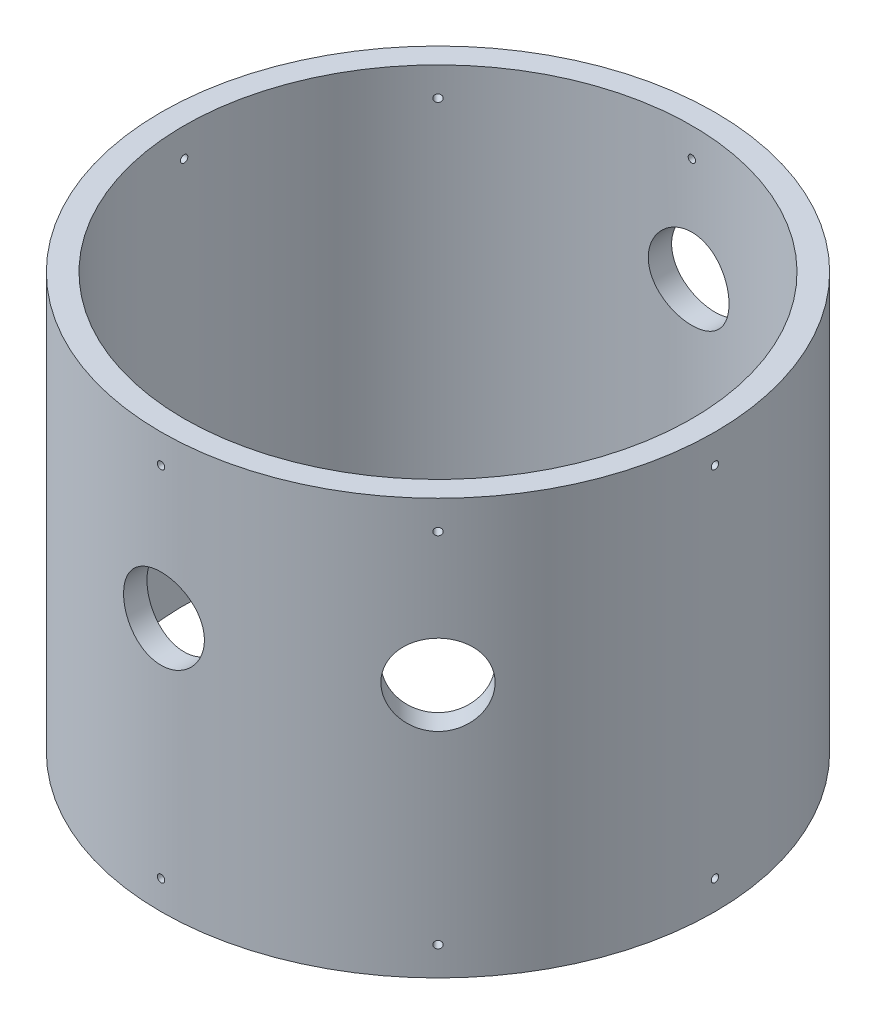
SolidWorks part; units mm, degrees
ref_plane "Front Plane" through (0, 0, 0) normal (0, 0, 1) x (1, 0, 0)
ref_plane "Top Plane" through (0, 0, 0) normal (0, 1, 0) x (1, 0, 0)
ref_plane "Right Plane" through (0, 0, 0) normal (1, 0, 0) x (0, 0, -1)
sketch "Sketch1" plane through (0, 0, 0) normal (0, 1, 0) x (1, 0, 0)
  circle A0 centre (0, 0) radius 152.4
  circle A1 centre (0, 0) radius 139.7
  dimension "D1" = 304.8
  dimension "D2" = 279.4
extrude "Boss-Extrude1" add sketch "Sketch1" along normal blind 228.6
ref_plane "Plane1" through (0, 0, 152.4) normal (0, 0, 1) x (1, 0, 0)
hole_wizard "#10-32 Tapped Hole1" positions "Sketch2" profile "Sketch3" tap size "#10-32" standard "ANSI Inch"
sketch "Sketch2" plane through (0, 0, 152.4) normal (0, 0, 1) x (1, 0, 0)
  line L0 (152.4, 228.6) -> (-152.4, 228.6) construction
  line L1 (-152.4, 0) -> (152.4, 0) construction
  line L3 (0, 212.725) -> (0, 15.875)
  line L4 (0, 15.875) -> (0, 0)
  point P0 (0, 212.725)
  point P2 (0, 15.875)
  dimension "D1" = 15.875
  dimension "D2" = 15.875
sketch "Sketch3" plane through (0, 212.725, 152.4) normal (1, 0, 0) x (0, -1, 0)
  line L0 (0, 0) -> (0, 349.967)
  line L1 (0, 349.967) -> (2.0193, 349.967)
  line L2 (2.0193, 349.967) -> (2.0193, 0)
  line L5 (2.0193, 0) -> (0, 0)
  line L11 (0, -6.35) -> (0, 107.95) construction
  dimension "Thread Major Dia." = 4.0386
  dimension "Thru Tap Drill Depth" = 349.967
pattern_circular "CirPattern1" count 8 over 360 about axis through (0, 228.6, 0) along (0, 1, 0) of "#10-32 Tapped Hole1"
ref_plane "Plane2" through (-107.7631, 0, 107.7631) normal (-0.7071, 0, 0.7071) x (0, -1, 0)
hole_wizard "Pressure Relief Hole" positions "Sketch4" profile "Sketch5" legacy
sketch "Sketch4" plane through (0, 0, 152.4) normal (0, 0, 1) x (1, 0, 0)
  line L0 (0, 139.7) -> (0, 0)
  point P0 (0, 139.7)
  dimension "D1" = 139.7
sketch "Sketch5" plane through (0, 139.7, 152.4) normal (1, 0, 0) x (0, -1, 0)
  line L0 (0, 0) -> (0, 12.7)
  line L1 (0, 12.7) -> (22.225, 12.7)
  line L2 (22.225, 12.7) -> (22.225, 0)
  line L3 (22.225, 0) -> (0, 0)
  line L4 (0, 110) -> (0, -10) construction
  dimension "Diameter" = 44.45
  dimension "Depth" = 12.7
ref_plane "Plane3" through (107.7631, 0, 107.7631) normal (0.7071, 0, 0.7071) x (0, -1, 0)
hole_wizard "Helium In" positions "Sketch6" profile "Sketch7" legacy
sketch "Sketch6" plane through (107.7631, 0, 107.7631) normal (0.7071, 0, 0.7071) x (0, -1, 0)
  line L0 (-139.7, 0) -> (0, 0)
  point P0 (-139.7, 0)
  dimension "D1" = 139.7
sketch "Sketch7" plane through (107.7631, 139.7, 107.7631) normal (0, 1, 0) x (0.7071, 0, -0.7071)
  line L0 (0, 0) -> (0, 12.7)
  line L1 (0, 12.7) -> (22.225, 12.7)
  line L2 (22.225, 12.7) -> (22.225, 0)
  line L3 (22.225, 0) -> (0, 0)
  line L4 (0, 110) -> (0, -10) construction
  dimension "Diameter" = 44.45
  dimension "Depth" = 12.7
ref_plane "Plane4" through (0, 0, -152.4) normal (0, 0, -1) x (-1, 0, 0)
hole_wizard "Vent Valve" positions "Sketch8" profile "Sketch9" legacy
sketch "Sketch8" plane through (0, 0, -152.4) normal (0, 0, -1) x (-1, 0, 0)
  line L0 (-152.4, 0) -> (152.4, 0) construction
  point P0 (0, 155.575)
  dimension "D1" = 155.575
sketch "Sketch9" plane through (0, 155.575, -152.4) normal (1, 0, 0) x (0, 1, 0)
  line L0 (0, 0) -> (0, 25.4)
  line L1 (0, 25.4) -> (22.225, 25.4)
  line L2 (22.225, 25.4) -> (22.225, 0)
  line L3 (22.225, 0) -> (0, 0)
  line L4 (0, 110) -> (0, -10) construction
  dimension "Diameter" = 44.45
  dimension "Depth" = 25.4
